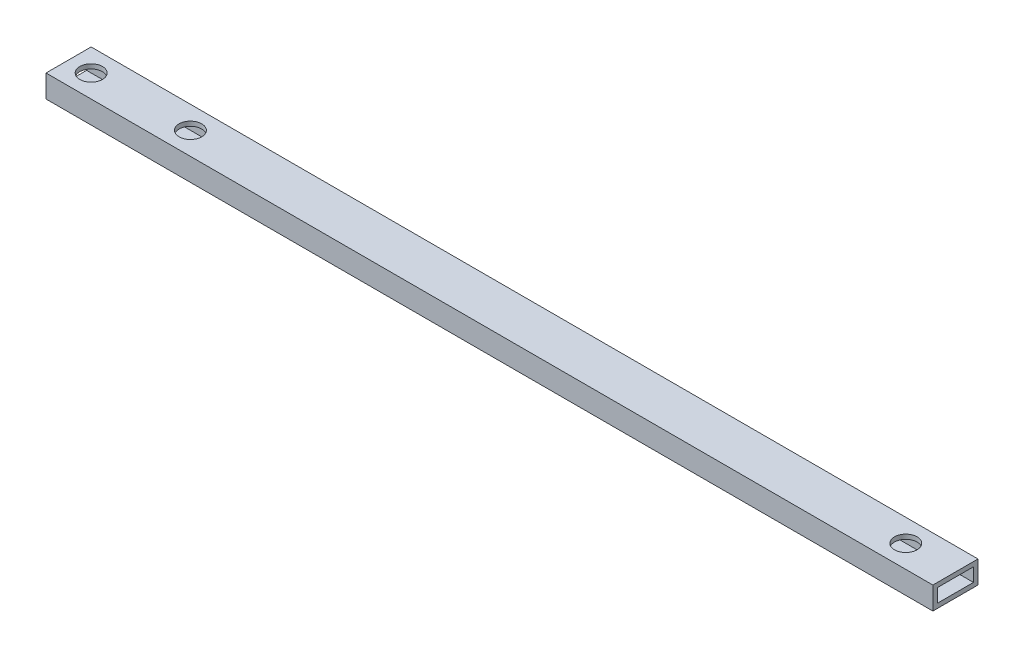
SolidWorks part; units mm, degrees
ref_plane "Alzado" through (0, 0, 0) normal (0, 0, 1) x (1, 0, 0)
ref_plane "Planta" through (0, 0, 0) normal (0, 1, 0) x (1, 0, 0)
ref_plane "Vista lateral" through (0, 0, 0) normal (1, 0, 0) x (0, 0, -1)
sketch "Croquis1" plane through (0, 0, 0) normal (1, 0, 0) x (0, 0, -1)
  line L1 (-5, -2.5) -> (5, -2.5)
  line L2 (-5, -2.5) -> (-5, 2.5)
  line L3 (-5, 2.5) -> (5, 2.5)
  line L4 (5, -2.5) -> (5, 2.5)
  line L5 (-5, -2.5) -> (5, 2.5) construction
  line L6 (-5, 2.5) -> (5, -2.5) construction
  line L7 (-4, -1.5) -> (4, -1.5)
  line L8 (-4, -1.5) -> (-4, 1.5)
  line L9 (-4, 1.5) -> (4, 1.5)
  line L10 (4, -1.5) -> (4, 1.5)
  line L11 (-4, -1.5) -> (4, 1.5) construction
  line L12 (-4, 1.5) -> (4, -1.5) construction
  point P0 (0, 0)
  point P6 (0, 0)
  dimension "D1" = 10
  dimension "D2" = 5
  dimension "D3" = 8
  dimension "D4" = 3
extrude "Saliente-Extruir1" add sketch "Croquis1" along normal blind 393
sketch "Croquis2" plane through (0, 2.5, 0) normal (0, 1, 0) x (1, 0, 0)
  line L0 (196.5, 5) -> (196.5, -5) construction
  line L1 (393, 5) -> (0, 5) construction
  line L2 (393, -5) -> (0, -5) construction
  line L3 (10, 0) -> (383, 0) construction
  line L4 (10, 0) -> (5, 0) construction
  line L5 (383, 0) -> (388, 0) construction
  circle A0 centre (5, 0) radius 2.5
  circle A1 centre (388, 0) radius 2.5
  circle A2 centre (27, 0) radius 2.5
  circle A3 centre (366, 0) radius 2.5
  circle A4 centre (207.5, 0) radius 2.5
  circle A5 centre (185.5, 0) radius 2.5
  point P10 (196.5, 0)
  dimension "D2" = 5
  dimension "D5" = 5
  dimension "D6" = 5
  dimension "D8" = 5
  dimension "D10" = 5
  dimension "D12" = 5
  dimension "D1" = 373
  dimension "D3" = 5
  dimension "D4" = 5
  dimension "D7" = 22
  dimension "D9" = 22
  dimension "D11" = 11
  dimension "D13" = 22
extrude "Cortar-Extruir1" cut sketch "Croquis2" against normal blind 5
sketch "Sketch1" plane through (0, 0, 5) normal (0, 0, 1) x (1, 0, 0)
  line L0 (393, 2.5) -> (0, 2.5) construction
  line L2 (196.5, 2.5) -> (393, 2.5)
  line L3 (196.5, 2.5) -> (196.5, -2.5)
  line L4 (196.5, -2.5) -> (393, -2.5)
  line L5 (393, 2.5) -> (393, -2.5)
extrude "Cut-Extrude1" cut sketch "Sketch1" against normal blind 10
